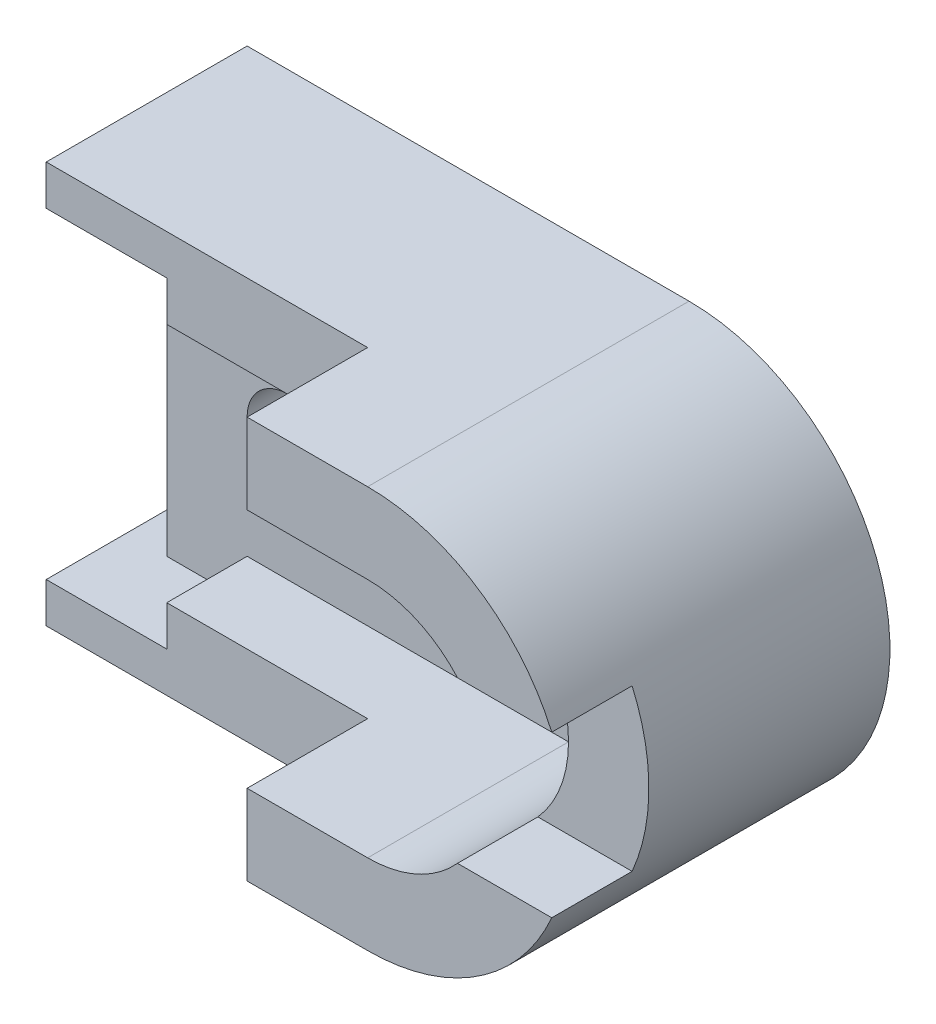
SolidWorks part; units mm, degrees
ref_plane "Front Plane" through (0, 0, 0) normal (0, 0, 1) x (1, 0, 0)
ref_plane "Top Plane" through (0, 0, 0) normal (0, 1, 0) x (1, 0, 0)
ref_plane "Right Plane" through (0, 0, 0) normal (1, 0, 0) x (0, 0, -1)
sketch "Sketch1" plane through (0, 0, 0) normal (0, 0, 1) x (1, 0, 0)
  line L0 (0, 0) -> (-30, 0)
  line L1 (-30, 0) -> (-30, 10)
  line L2 (-30, 10) -> (50, 10)
  line L3 (50, 10) -> (50, -10)
  line L4 (50, -10) -> (0, -10)
  line L5 (0, -10) -> (0, 0)
  dimension "D1" = 30
  dimension "D2" = 10
  dimension "D3" = 80
  dimension "D4" = 20
extrude "Boss-Extrude1" add sketch "Sketch1" along normal blind 50
sketch "Sketch2" plane through (0, 0, 0) normal (0, 0, -1) x (-1, 0, 0)
  line L0 (0, -10) -> (0, 0)
  line L1 (0, 0) -> (20, 0)
  line L2 (20, 0) -> (20, -80)
  line L3 (20, -80) -> (0, -80)
  line L4 (0, -80) -> (0, -70)
  line L5 (0, -70) -> (-80, -70)
  line L6 (0, -10) -> (-80, -10)
  arc A0 (-80, -10) -> (-80, -70) centre (-80, -40) ccw
  line M1 (0, -10) -> (0, 0)
  line M2 (0, 0) -> (30, 0)
  line M6 (-50, -10) -> (0, -10)
  dimension "D1" = 30
  dimension "D2" = 20
  dimension "D3" = 80
  dimension "D4" = 20
  dimension "D5" = 10
  dimension "D6" = 80
  dimension "D7" = 80
extrude "Boss-Extrude2" add sketch "Sketch2" against normal blind 30 contours L6 A0 L5 L4 L3 L2 M2 M1 M6
sketch "Sketch3" plane through (0, 0, 0) normal (0, 0, -1) x (-1, 0, 0)
  line L0 (0, -70) -> (0, -80)
  line L1 (0, -80) -> (30, -80)
  line L2 (0, -70) -> (-50, -70)
  line L3 (0, -70) -> (-80, -70) construction
  line L4 (-50, -70) -> (-50, -90)
  line L5 (-50, -90) -> (30, -90)
  line L6 (30, -90) -> (30, -80)
  dimension "D1" = 30
  dimension "D2" = 10
  dimension "D3" = 80
extrude "Boss-Extrude3" add sketch "Sketch3" against normal blind 50
sketch "Sketch4" plane through (0, 0, 30) normal (0, 0, 1) x (1, 0, 0)
  line L0 (80, -90) -> (50, -90)
  line L1 (80, 10) -> (50, 10)
  line L3 (80, -10) -> (50, -10)
  line L4 (50, -10) -> (80, -10) construction
  line L5 (50, -10) -> (50, 10)
  line L6 (80, -70) -> (50, -70)
  line L7 (50, -70) -> (50, -90)
  arc A0 (80, -10) -> (80, -70) centre (80, -40) cw
  arc A1 (80, -70) -> (80, -10) centre (80, -40) ccw construction
  arc A2 (80, 10) -> (80, -90) centre (80, -40) cw
  dimension "D1" = 20
  dimension "D2" = 30
  dimension "D3" = 30
  dimension "D4" = 30
  dimension "D5" = 30
  dimension "D6" = 30
  dimension "D7" = 20
  dimension "D8" = 20
  dimension "D9" = 30
extrude "Boss-Extrude7" add sketch "Sketch4" along normal blind 50 and the other way blind 30
sketch "Sketch5" plane through (0, 0, 0) normal (1, 0, 0) x (0, 0, -1)
  line L1 (-80, -20) -> (-60, -20)
  line L2 (-80, -20) -> (-80, -60)
  line L3 (-80, -60) -> (-60, -60)
  line L4 (-60, -20) -> (-60, -60)
  dimension "D1" = 20
  dimension "D2" = 0
  dimension "D3" = 40
  dimension "D4" = 30
extrude "Cut-Extrude1" cut sketch "Sketch5" along normal blind 211
sketch "Sketch6" plane through (0, 0, 30) normal (0, 0, 1) x (1, 0, 0)
  line L0 (10, -30) -> (20, -30)
  line L1 (10, -50) -> (20, -50)
  arc A0 (10, -30) -> (10, -50) centre (10, -40) ccw
  arc A1 (20, -30) -> (20, -50) centre (20, -40) cw
  dimension "D1" = 10
  dimension "D5" = 30
  dimension "D6" = 10
  dimension "D2" = 20
  dimension "D3" = 20
  dimension "D4" = 30
  dimension "D7" = 10
  dimension "D8" = 10
  dimension "D9" = 20
  dimension "D10" = 10
extrude "Cut-Extrude2" cut sketch "Sketch6" against normal blind 211
sketch "Sketch7" plane through (0, 0, 30) normal (0, 0, 1) x (1, 0, 0)
  line L0 (70, -30) -> (60, -30)
  line L1 (60, -50) -> (70, -50)
  arc A0 (60, -30) -> (60, -50) centre (60, -40) ccw
  arc A1 (70, -30) -> (70, -50) centre (70, -40) cw
  dimension "D1" = 10
  dimension "D6" = 10
  dimension "D2" = 40
  dimension "D3" = 0
  dimension "D4" = 40
  dimension "D5" = 90
  dimension "D7" = 10
  dimension "D8" = 10
  dimension "D9" = 10
  dimension "D10" = 10
extrude "Cut-Extrude3" cut sketch "Sketch7" against normal blind 211
